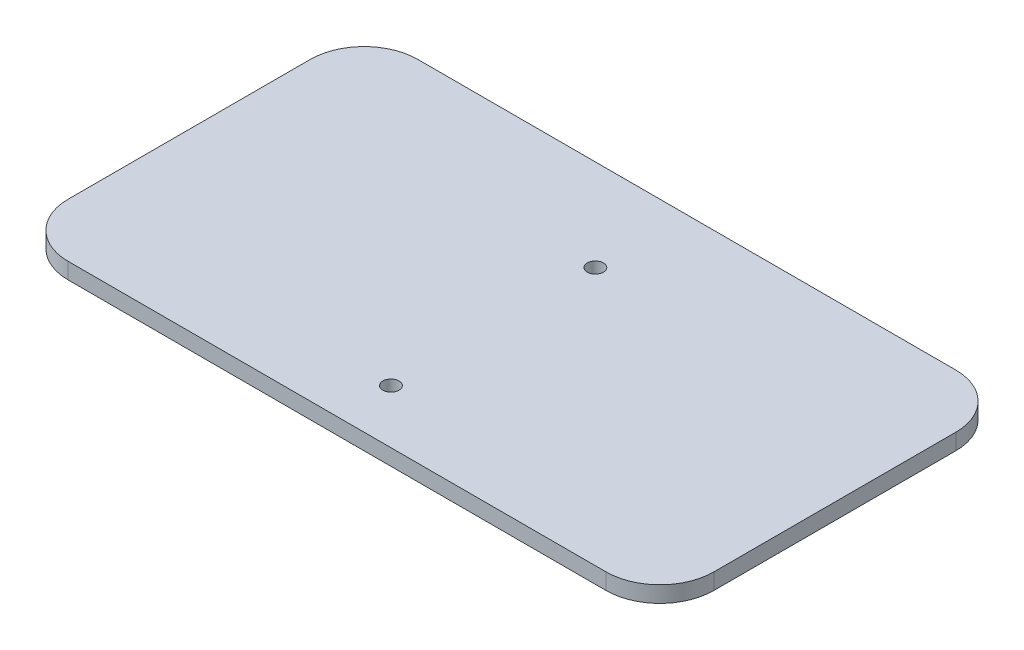
SolidWorks part; units mm, degrees
ref_plane "Front Plane" through (0, 0, 0) normal (0, 0, 1) x (1, 0, 0)
ref_plane "Top Plane" through (0, 0, 0) normal (0, 1, 0) x (1, 0, 0)
ref_plane "Right Plane" through (0, 0, 0) normal (1, 0, 0) x (0, 0, -1)
sketch "Sketch1" plane through (0, 0, 0) normal (0, 1, 0) x (1, 0, 0)
  line L1 (-50, -10) -> (50, -10)
  line L2 (-60, 0) -> (-60, 45)
  line L3 (-50, 55) -> (50, 55)
  line L4 (60, 0) -> (60, 45)
  line L5 (-60, -10) -> (60, 55) construction
  line L6 (-60, 55) -> (60, -10) construction
  circle A0 centre (0, 0) radius 1.5
  circle A1 centre (0, 38) radius 1.5
  arc A2 (-60, 45) -> (-50, 55) centre (-50, 45) cw
  arc A3 (50, 55) -> (60, 45) centre (50, 45) cw
  arc A4 (50, -10) -> (60, 0) centre (50, 0) ccw
  arc A5 (-50, -10) -> (-60, 0) centre (-50, 0) cw
  point P9 (0, 22.5)
  point P10 (0, 0)
  point P11 (0, 0)
  dimension "D2" = 3
  dimension "D3" = 3
  dimension "D7" = 10
  dimension "D1" = 38
  dimension "D4" = 120
  dimension "D5" = 65
  dimension "D6" = 10
extrude "Boss-Extrude1" add sketch "Sketch1" along normal blind 3
